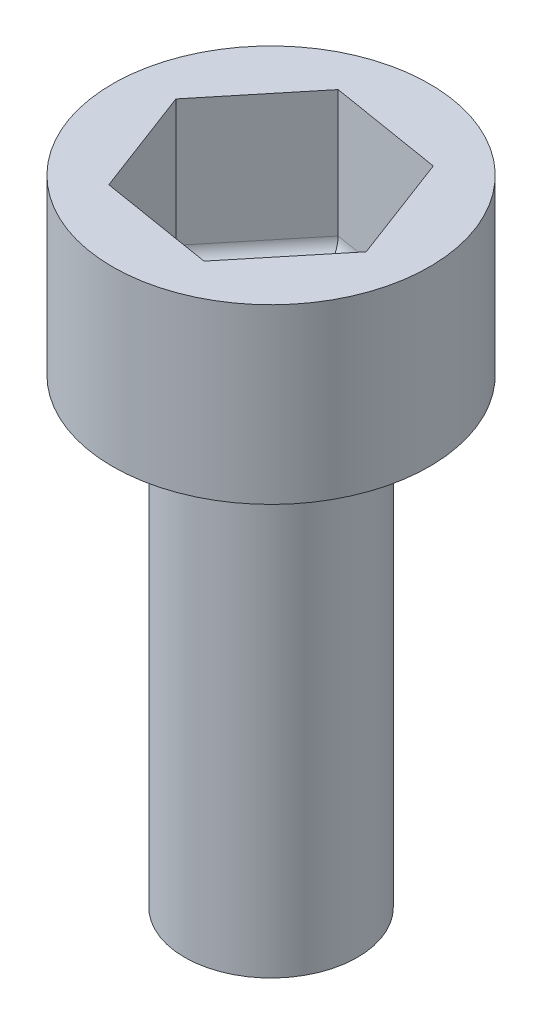
SolidWorks part; units mm, degrees
ref_plane "前视基准面" through (0, 0, 0) normal (0, 0, 1) x (1, 0, 0)
ref_plane "上视基准面" through (0, 0, 0) normal (0, 1, 0) x (1, 0, 0)
ref_plane "右视基准面" through (0, 0, 0) normal (1, 0, 0) x (0, 0, -1)
sketch "草图1" plane through (0, 0, 0) normal (0, 1, 0) x (1, 0, 0)
  circle A0 centre (0, 0) radius 1.5
  dimension "D1" = 3
extrude "凸台-拉伸1" add sketch "草图1" along normal blind 8
sketch "草图2" plane through (0, 8, 0) normal (0, 1, 0) x (1, 0, 0)
  circle A0 centre (0, 0) radius 2.75
extrude "凸台-拉伸2" add sketch "草图2" along normal blind 3
sketch "草图3" plane through (0, 11, 0) normal (0, 1, 0) x (1, 0, 0)
  line L1 (1.9737, -0.3231) -> (1.2667, 1.5478)
  line L2 (1.2667, 1.5478) -> (-0.7071, 1.8708)
  line L3 (-0.7071, 1.8708) -> (-1.9737, 0.3231)
  line L4 (-1.9737, 0.3231) -> (-1.2667, -1.5478)
  line L5 (-1.2667, -1.5478) -> (0.7071, -1.8708)
  line L6 (0.7071, -1.8708) -> (1.9737, -0.3231)
  circle A0 centre (0, 0) radius 1.7321 construction
  dimension "D1" = 2
extrude "切除-拉伸1" cut sketch "草图3" against normal blind 2.5
fillet "圆角1" radius 0.3 6 edges at (1.3404, 8.5, 1.097) (-0.2798, 8.5, 1.7093) (-1.6202, 8.5, 0.6123) (1.6202, 8.5, -0.6123) (-1.3404, 8.5, -1.097) (0.2798, 8.5, -1.7093)
